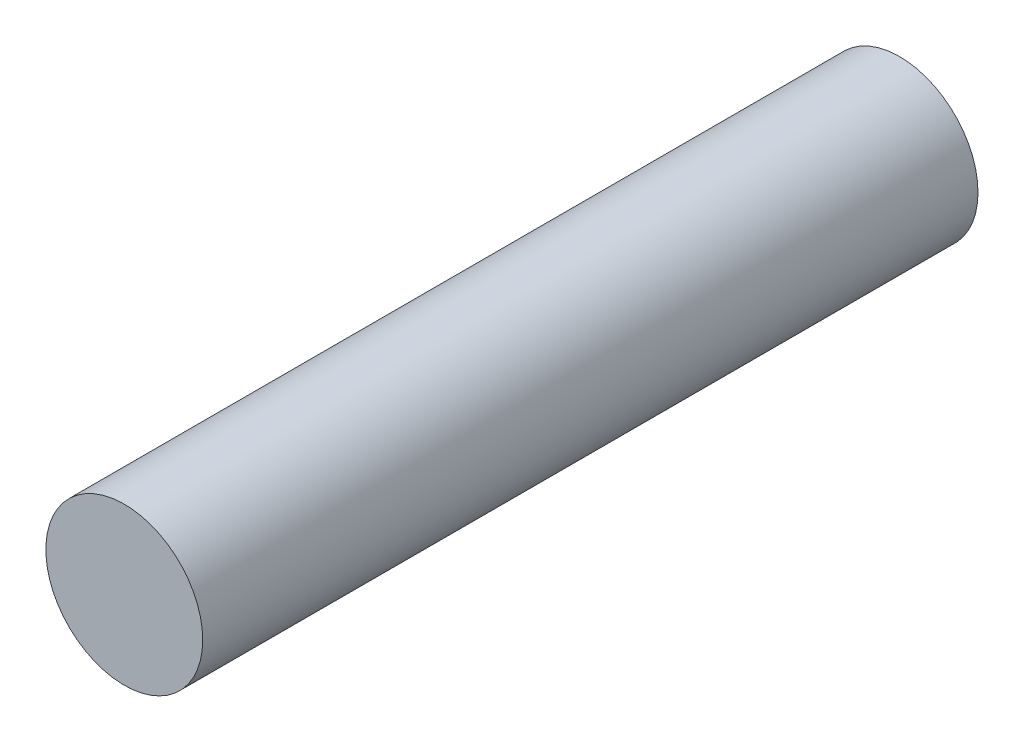
SolidWorks part; units mm, degrees
ref_plane "Front Plane" through (0, 0, 0) normal (0, 0, 1) x (1, 0, 0)
ref_plane "Top Plane" through (0, 0, 0) normal (0, 1, 0) x (1, 0, 0)
ref_plane "Right Plane" through (0, 0, 0) normal (1, 0, 0) x (0, 0, -1)
sketch "Sketch1" plane through (0, 0, 0) normal (0, 0, 1) x (1, 0, 0)
  circle A0 centre (0, 0) radius 3.302
  dimension "D1" = 6.604
extrude "Extrude1" add sketch "Sketch1" along normal blind 32.639
